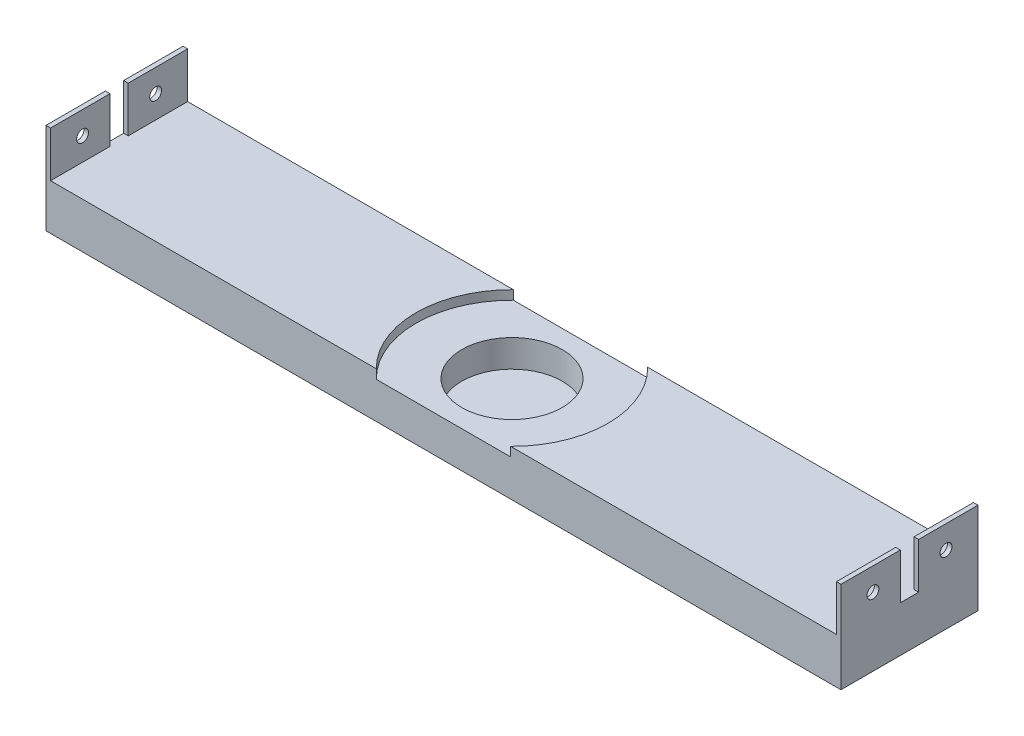
SolidWorks part; units mm, degrees
ref_plane "Front Plane" through (0, 0, 0) normal (0, 0, 1) x (1, 0, 0)
ref_plane "Top Plane" through (0, 0, 0) normal (0, 1, 0) x (1, 0, 0)
ref_plane "Right Plane" through (0, 0, 0) normal (1, 0, 0) x (0, 0, -1)
sketch "Sketch1" plane through (0, 0, 0) normal (0, 0, 1) x (1, 0, 0)
  line L0 (0, 1.2177) -> (0, 0) construction
  line L1 (-87, 20) -> (-87, 0)
  line L2 (-87, 0) -> (87, 0)
  line L4 (86, 10) -> (-86, 10)
  line L5 (-86, 10) -> (-86, 20)
  line L6 (-86, 20) -> (-87, 20)
  line L7 (86, 20) -> (87, 20)
  line L8 (86, 10) -> (86, 20)
  line L9 (87, 20) -> (87, 0)
  dimension "D1" = 1
  dimension "D2" = 20
  dimension "D3" = 10
  dimension "D4" = 87
extrude "Boss-Extrude1" add sketch "Sketch1" along normal blind 30
sketch "Sketch2" plane through (0, 10, 0) normal (0, 1, 0) x (1, 0, 0)
  line L0 (0, 0) -> (0, -52.4511) construction
  line L1 (86, 0) -> (-86, 0) construction
  circle A0 centre (0, -15) radius 11
  dimension "D1" = 22
  dimension "D2" = 15
extrude "Cut-Extrude1" cut sketch "Sketch2" against normal blind 8
sketch "Sketch3" plane through (87, 0, 0) normal (1, 0, 0) x (0, 0, -1)
  line L0 (-15, 20) -> (-15, -1.3605)
  line L1 (-30, 20) -> (0, 20) construction
  line L2 (-30, 0) -> (-30, 20) construction
  line L3 (-30, 10) -> (0.3844, 10) construction
  circle A0 centre (-23, 15) radius 1.3
  circle A1 centre (-7, 15) radius 1.3
  dimension "D1" = 2.6
  dimension "D2" = 5
  dimension "D3" = 8
extrude "Cut-Extrude2" cut sketch "Sketch3" against normal through all both and the other way through all contours A0 | A1
sketch "Sketch4" plane through (-87, 0, 0) normal (-1, 0, 0) x (0, 0, 1)
  line L0 (15, 20) -> (15, 9.9277) construction
  line L1 (30, 20) -> (0, 20) construction
  line L2 (13, 20) -> (13, 10)
  line L3 (13, 10) -> (17, 10)
  line L4 (17, 10) -> (17, 20)
  line L5 (17, 20) -> (13, 20)
  dimension "D1" = 2
  dimension "D2" = 2
  dimension "D3" = 10
extrude "Cut-Extrude3" cut sketch "Sketch4" against normal through all both and the other way through all
sketch "Sketch5" plane through (0, 10, 0) normal (0, 1, 0) x (1, 0, 0)
  circle A0 centre (0, -15) radius 21
  circle A1 centre (0, -15) radius 11 construction
  dimension "D1" = 42
extrude "Cut-Extrude4" cut sketch "Sketch5" against normal blind 2
